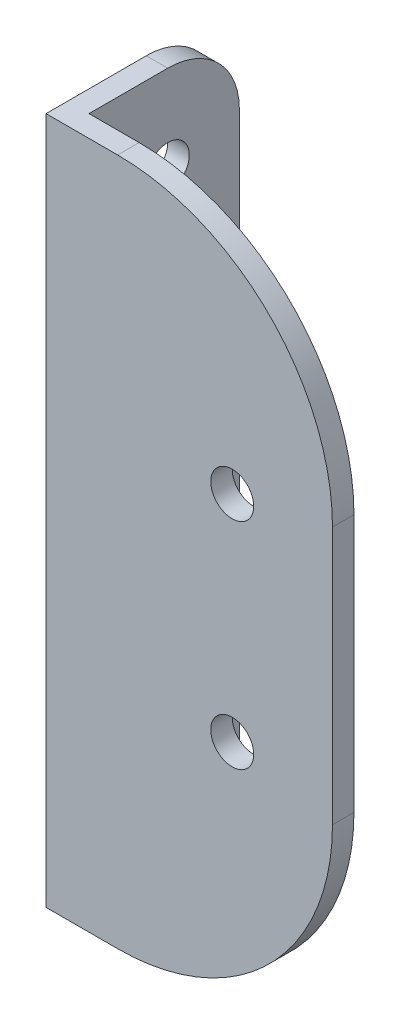
SolidWorks part; units mm, degrees
ref_plane "Front Plane" through (0, 0, 0) normal (0, 0, 1) x (1, 0, 0)
ref_plane "Top Plane" through (0, 0, 0) normal (0, 1, 0) x (1, 0, 0)
ref_plane "Right Plane" through (0, 0, 0) normal (1, 0, 0) x (0, 0, -1)
sketch "Sketch1" plane through (0, 0, 0) normal (0, 1, 0) x (1, 0, 0)
  line L0 (0, 0) -> (0, 12)
  line L1 (0, 0) -> (20, 0)
  line L2 (0, 12) -> (1.5, 12)
  line L3 (1.5, 12) -> (1.5, 1.5)
  line L4 (1.5, 1.5) -> (20, 1.5)
  line L5 (20, 1.5) -> (20, 0)
  dimension "D1" = 1.5
  dimension "D2" = 1.5
  dimension "D3" = 12
  dimension "D4" = 20
extrude "Boss-Extrude1" add sketch "Sketch1" along normal blind 48
sketch "Sketch2" plane through (0, 0, 0) normal (0, 0, 1) x (1, 0, 0)
  line L0 (13, 50.0118) -> (13, -2.9717) construction
  circle A0 centre (13, 31.5) radius 1.5
  circle A1 centre (13, 16.5) radius 1.5
  dimension "D1" = 3
  dimension "D2" = 3
  dimension "D3" = 13
  dimension "D4" = 15
  dimension "D5" = 16.5
extrude "Cut-Extrude1" cut sketch "Sketch2" against normal through all
sketch "Sketch3" plane through (0, 0, 0) normal (1, 0, 0) x (0, 0, -1)
  line L0 (7, 50.7157) -> (7, -2.7157) construction
  circle A0 centre (7, 42) radius 1.5
  circle A1 centre (7, 24) radius 3
  circle A2 centre (7, 6) radius 1.5
  dimension "D2" = 6
  dimension "D3" = 3
  dimension "D4" = 3
  dimension "D1" = 7
  dimension "D5" = 18
  dimension "D6" = 18
  dimension "D7" = 6
extrude "Cut-Extrude3" cut sketch "Sketch3" along normal through all
fillet "Fillet1" radius 5 2 edges at (0.75, 0, -12) (0.75, 48, -12)
fillet "Fillet2" radius 15 2 edges at (20, 0, -0.75) (20, 48, -0.75)
